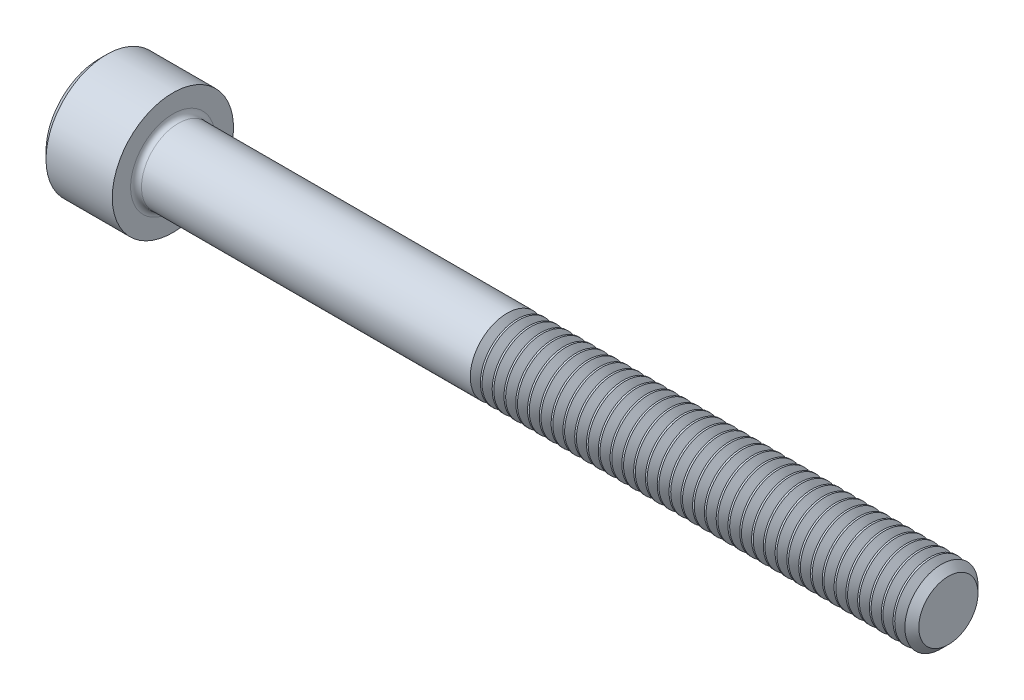
SolidWorks part; units mm, degrees
material "Plain Carbon Steel"
ref_plane "Plane1" through (0, 0, 0) normal (0, 0, 1) x (1, 0, 0)
ref_plane "Plane2" through (0, 0, 0) normal (0, 1, 0) x (1, 0, 0)
ref_plane "Plane3" through (0, 0, 0) normal (1, 0, 0) x (0, 0, -1)
sketch "BodySke" plane through (0, 0, 0) normal (0, 0, 1) x (1, 0, 0)
  line L0 (0, 0) -> (0, 3.4862)
  line L1 (0.4826, 3.9687) -> (4.826, 3.9687)
  line L2 (4.826, 3.9687) -> (4.826, 2.413)
  line L3 (4.826, 2.413) -> (55.1536, 2.413)
  line L4 (55.626, 1.9406) -> (55.626, 0)
  line L5 (55.626, 0) -> (0, 0)
  line L6 (-31.75, 0) -> (127, 0) construction
  line L7 (0, 3.4862) -> (0.4826, 3.9687)
  line L8 (55.626, 1.9406) -> (55.1536, 2.413)
  line L9 (0, -3.4862) -> (0.4826, -3.9688) construction
  line L10 (55.626, -1.9406) -> (55.1536, -2.413) construction
  line L11 (5.6185, 9.525) -> (5.6185, 3.175) construction
  line L12 (27.051, 9.525) -> (27.051, 3.175) construction
  line L13 (17.526, 9.525) -> (17.526, 3.175) construction
  dimension "Diameter" = 4.826
  dimension "Head_ht" = 4.826
  dimension "Length" = 50.8
  dimension "Body_ch_ang" = 45
  dimension "Head_dia" = 7.9375
  dimension "Head_ch_ang" = 45
  dimension "Head_side_ht" = 4.3434
  dimension "Minor_dia" = 3.8811
  dimension "Advance" = 0.7925
  dimension "Thread_nom" = 28.575
  dimension "Thread_length" = 38.1
revolve "Base-Revolve" add sketch "BodySke"
cosmetic thread "ThreadCosmetic" [suppressed]
fillet "Fillet1" radius 0.3556 1 edges at (4.826, 0, 2.413)
sketch "Sketch2" plane through (0, 0, 0) normal (0, 0, 1) x (1, 0, 0)
  line L0 (0, 1.985) -> (2.286, 1.985)
  line L1 (2.286, 1.985) -> (3.432, 0)
  line L2 (-31.75, 0) -> (127, 0) construction
  line L3 (3.432, 0) -> (0, 0)
  line L4 (0, 0) -> (0, 1.985)
  line L5 (0, 3.4862) -> (0, -3.4862) construction
  line L6 (0, 0) -> (47.625, 0) construction
  line L7 (4.826, -3.9687) -> (4.826, 3.9687) construction
  dimension "D1" = 1.985
  dimension "D2" = 60
  dimension "Wall_thickness" = 2.54
revolve "Hex-PreBroach" cut sketch "Sketch2" angle 360 about L6
sketch "Sketch3" plane through (0, 0, 0) normal (-1, 0, 0) x (0, 0.5, 0.866)
  line L0 (1.146, 1.985) -> (-1.146, 1.985)
  line L1 (-1.146, 1.985) -> (-2.2921, 0)
  line L2 (1.146, 1.985) -> (2.2921, 0)
  line L3 (1.146, -1.985) -> (2.2921, 0)
  line L4 (1.146, -1.985) -> (-1.146, -1.985)
  line L5 (-1.146, -1.985) -> (-2.2921, 0)
  dimension "D1" = 1.985
  dimension "D2" = 1.985
  dimension "Hex_size" = 3.97
extrude "Hex" cut sketch "Sketch3" against normal blind 2.286
sketch "Sketch4" plane through (0, 0, 0) normal (-1, 0, 0) x (0, 0, 1)
  line L0 (0, 0) -> (2.3876, 0)
  line L1 (0, 0) -> (6.1484, 3.5498) construction
  line L2 (0, 0) -> (1.1938, 2.0677)
  line L3 (1.9883, 0.576) -> (2.2704, 0.7389)
  line L4 (1.493, 1.4339) -> (1.7751, 1.5968)
  arc A0 (1.9883, 0.576) -> (1.493, 1.4339) centre (0, 0) ccw
  arc A1 (2.3876, 0) -> (2.2704, 0.7389) centre (0, 0) ccw
  arc A2 (1.1938, 2.0677) -> (1.7751, 1.5968) centre (0, 0) cw
  dimension "D1" = 30
  dimension "Spline_n_dim" = 4.1402
  dimension "Spline_m_dim" = 4.7752
  dimension "D2" = 60
  dimension "D3" = 0.4953
  dimension "Spline_p_dim" = 0.9906
extrude "Spline" [suppressed] cut sketch "Sketch4" against normal blind 2.286
pattern_circular "CirPattern1" [suppressed] count 6 every 60
sketch "Sketch5" plane through (0, 0, 0) normal (0, 0, 1) x (1, 0, 0)
  line L0 (-31.75, 0) -> (127, 0) construction
  line L2 (0, 3.4862) -> (0, -3.4862) construction
  circle A0 centre (1.651, 0) radius 0.5905
  dimension "Drilled_hole_dia" = 1.1811
  dimension "Drilled_hole_loc" = 1.651
extrude "Hole" [suppressed] cut sketch "Sketch5" against normal through all and the other way through all
pattern_circular "Drilled-4" [suppressed] count 2 every 60
pattern_circular "Drilled-6" [suppressed] count 3 every 60
sketch "ThdSchSke" plane through (0, 0, 0) normal (0, 0, 1) x (1, 0, 0)
  line L0 (27.051, -1.9406) -> (26.7202, -2.413)
  line L1 (27.051, -1.9406) -> (27.3818, -2.413)
  line L2 (27.3818, -2.413) -> (27.3818, -3.0163)
  line L3 (-3.175, 0) -> (5.1513, 0) construction
  line L5 (27.3818, -3.0163) -> (26.7202, -3.0163)
  line L6 (26.7202, -3.0163) -> (26.7202, -2.413)
  line L7 (0, 3.4862) -> (0, -3.4862) construction
  dimension "Thread_minor" = 3.8811
  dimension "Diameter" = 4.826
  dimension "Start" = 27.051
  dimension "SideAngle" = 55
  dimension "VeeAngle" = 70
  dimension "Overcut" = 6.0325
revolve "ThreadSchematic" cut sketch "ThdSchSke" angle 360 about L3
pattern_linear "ThdSchPat" count 37 spacing 0.7723 along (1, 0, 0) of "ThreadSchematic"
equation "\"D2@Sketch3\" = \"Hex_size@Sketch3\" / 2"
equation "\"D1@Sketch3\" = \"Hex_size@Sketch3\" / 2"
equation "\"D1@Sketch2\" = \"Hex_size@Sketch3\" / 2"
equation "\"D3@Sketch4\" = \"Spline_p_dim@Sketch4\" / 2"
equation "\"Thread_minor@ThreadCosmetic\"  =  \"Minor_dia@BodySke\""
equation "\"D2@CirPattern1\" = 360 / \"Num_teeth@CirPattern1\""
equation "\"Wall_thickness@Sketch2\" = \"Head_ht@BodySke\" - \"Key_eng@Hex\""
equation "\"Thread_length@ThreadCosmetic\" = ((sgn( (\"Length@BodySke\" - \"Advance@BodySke\" ) - \"Thread_nom@BodySke\" )-1)*( (\"Length@BodySke\" - \"Advance@BodySke\" ) - \"Thread_nom@BodySke\" ))/-2+ \"Thread_nom@BodySke\""
equation "\"Thread_minor@ThdSchSke\" = \"Minor_dia@BodySke\""
equation "\"Diameter@ThdSchSke\" = \"Diameter@BodySke\""
equation "\"Overcut@ThdSchSke\" = \"Diameter@BodySke\" * 1.25"
equation "\"Start@ThdSchSke\" = \"Head_ht@BodySke\" + \"Length@BodySke\" - \"Thread_length@ThreadCosmetic\"  '---Non-countersunk---"
equation "\"Num_threads@ThdSchPat\" = int( \"Thread_length@ThreadCosmetic\" / \"Advance@BodySke\" + 0.999 )  + 1"
equation "\"Advance@ThdSchPat\" = \"Thread_length@ThreadCosmetic\" /  (\"Num_threads@ThdSchPat\" - 1) 'relax it"
equation "\"Num_threads@ThdSchPat\" = \"Num_threads@ThdSchPat\" - sgn( \"Num_threads@ThdSchPat\" - 1) '---chamfered tips only---"
